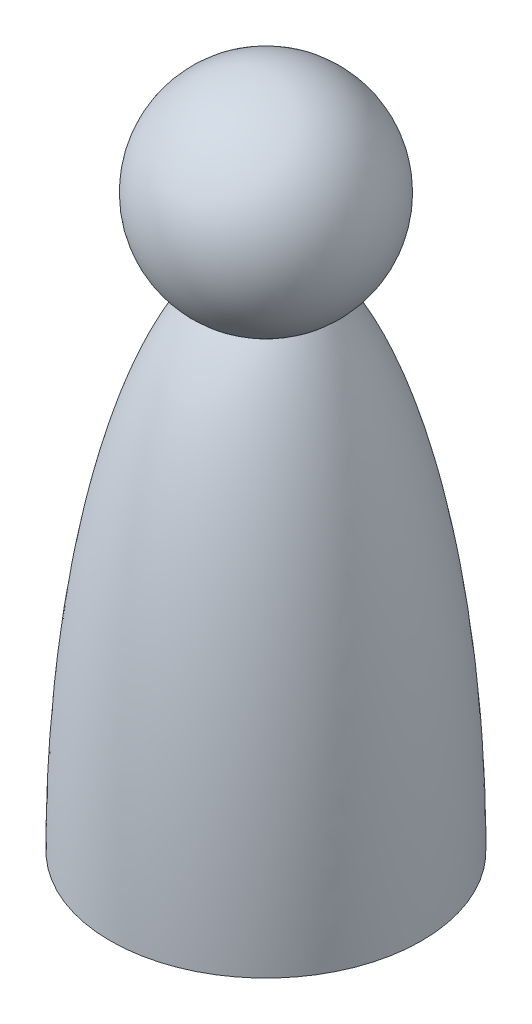
SolidWorks part; units mm, degrees
material "Beech"
ref_plane "Front Plane" through (0, 0, 0) normal (0, 0, 1) x (1, 0, 0)
ref_plane "Top Plane" through (0, 0, 0) normal (0, 1, 0) x (1, 0, 0)
ref_plane "Right Plane" through (0, 0, 0) normal (1, 0, 0) x (0, 0, -1)
sketch "Sketch1" plane through (0, 0, 0) normal (0, 0, 1) x (1, 0, 0)
  line L0 (-19.05, 0) -> (-12.7, 0)
  line L1 (0, -3.683) -> (0, 69.85)
  line L2 (0, 69.85) -> (0, 82.55)
  line L3 (0, 0) -> (0, -63.5) construction
  line L4 (0, -3.683) -> (-12.7, -3.683)
  line L5 (-12.7, -3.683) -> (-12.7, 0)
  arc A0 (0, 82.55) -> (-6.9002, 59.188) centre (0, 69.85) ccw
  ellipse E0 centre (0, 0) end of major axis (0, -63.5) minor radius 19.05 (19.05, 0) -> (0, 63.5) ccw construction
  ellipse E1 centre (0, 0) end of major axis (0, -63.5) minor radius 19.05 (-6.9002, 59.188) -> (-19.05, 0) ccw
  dimension "D2" = 25.4
  dimension "D1" = 38.1
  dimension "D3" = 69.85
  dimension "D4" = 63.5
  dimension "D5" = 12.7
  dimension "D6" = 3.683
revolve "Revolve1" add sketch "Sketch1" angle 360 about L3
